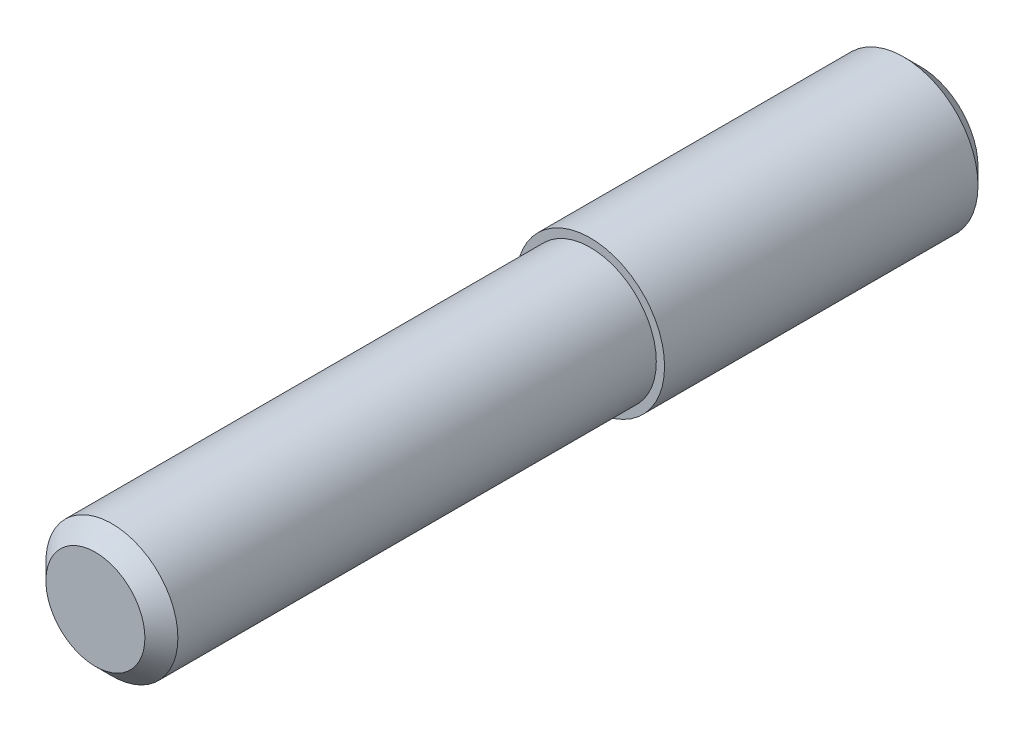
SolidWorks part; units mm, degrees
ref_plane "Plan de face" through (0, 0, 0) normal (0, 0, 1) x (1, 0, 0)
ref_plane "Plan de dessus" through (0, 0, 0) normal (0, 1, 0) x (1, 0, 0)
ref_plane "Plan de droite" through (0, 0, 0) normal (1, 0, 0) x (0, 0, -1)
sketch "Esquisse1" plane through (0, 0, 0) normal (0, 0, 1) x (1, 0, 0)
  circle A0 centre (0, 0) radius 4.5
  dimension "D1" = 9
extrude "Boss.-Extru.2" add sketch "Esquisse1" along normal blind 20
cosmetic thread "Représentation de filetage4" parameters "D1"=20, "D2"=6.619
sketch "Esquisse2" plane through (0, 0, 20) normal (0, 0, 1) x (1, 0, 0)
  circle A0 centre (0, 0) radius 4
  dimension "D1" = 8
extrude "Boss.-Extru.3" add sketch "Esquisse2" along normal blind 30
cosmetic thread "Représentation de filetage3" parameters "D1"=15, "D2"=6.619
chamfer "Chanfrein1" distance 1 2 edges at (4.5, 0, 0) (4, 0, 50)
